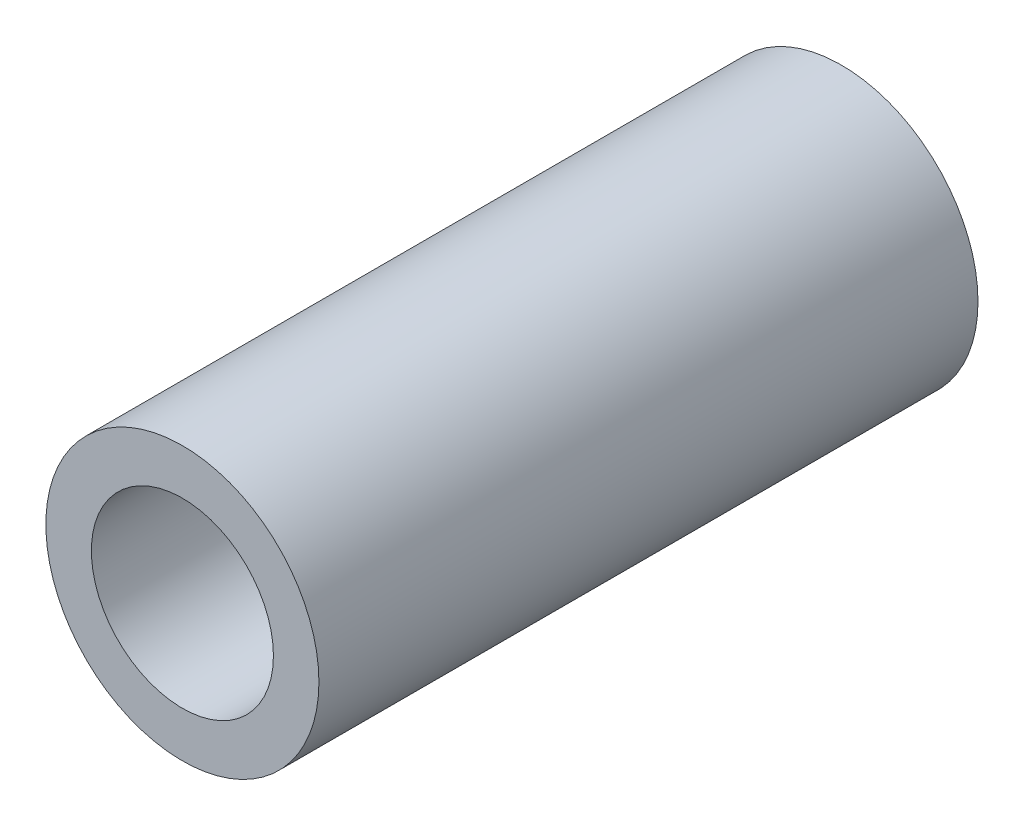
SolidWorks part; units mm, degrees
ref_plane "Front" through (0, 0, 0) normal (0, 0, 1) x (1, 0, 0)
ref_plane "Top" through (0, 0, 0) normal (0, 1, 0) x (1, 0, 0)
ref_plane "Right" through (0, 0, 0) normal (1, 0, 0) x (0, 0, -1)
sketch "Sketch1" plane through (0, 0, 0) normal (0, 0, 1) x (1, 0, 0)
  circle A0 centre (0, 0) radius 6.35
  circle A1 centre (0, 0) radius 9.525
  dimension "D1" = 12.7
  dimension "D2" = 3.175
extrude "Boss-Extrude1" add sketch "Sketch1" along normal blind 45.974
